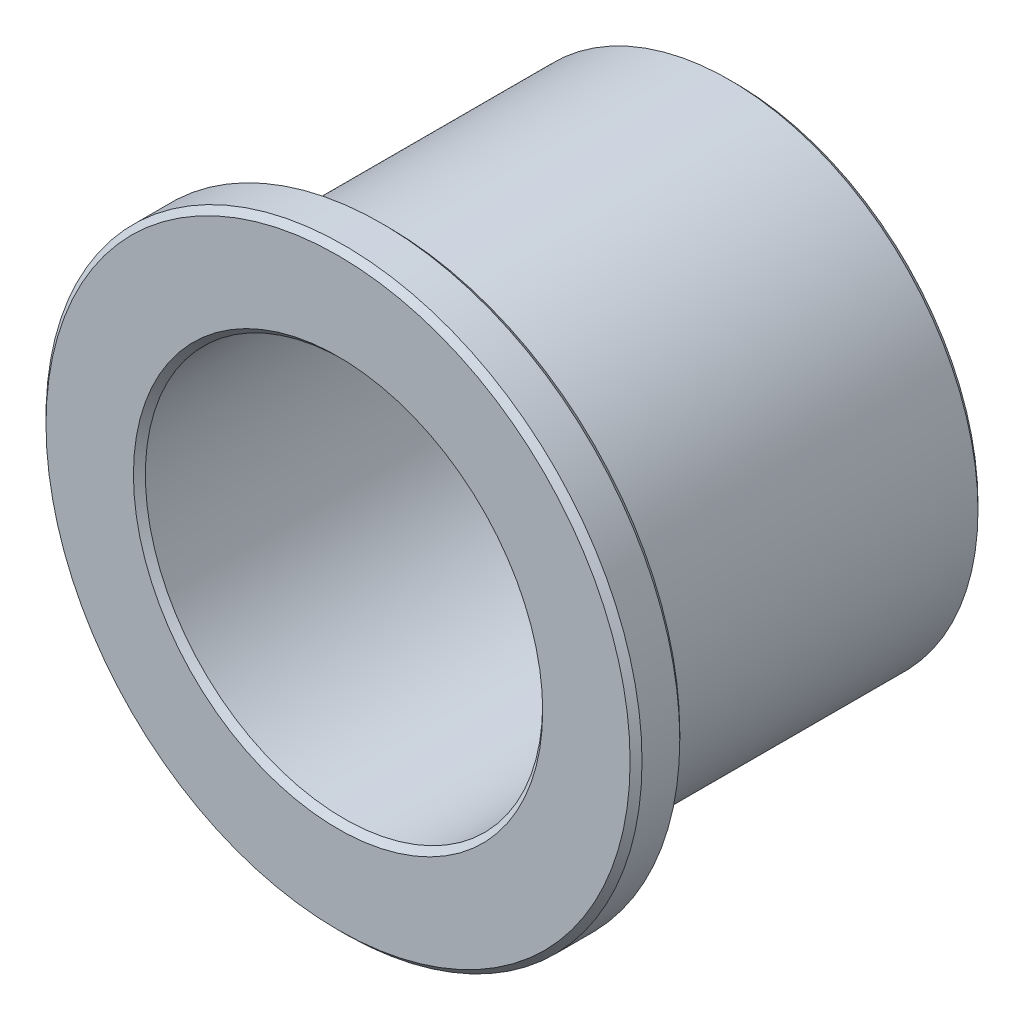
SolidWorks part; units mm, degrees
ref_plane "Front" through (0, 0, 0) normal (0, 0, 1) x (1, 0, 0)
ref_plane "Top" through (0, 0, 0) normal (0, 1, 0) x (1, 0, 0)
ref_plane "Right" through (0, 0, 0) normal (1, 0, 0) x (0, 0, -1)
sketch "Sketch1" plane through (0, 0, 0) normal (0, 0, 1) x (1, 0, 0)
  circle A0 centre (0, 0) radius 12.7
  circle A1 centre (0, 0) radius 15.8877
  circle A2 centre (0, 0) radius 19.05
  dimension "ID" = 25.4
  dimension "OD" = 31.7754
  dimension "Flange OD" = 38.1
sketch "Sketch2" plane through (0, 0, 0) normal (1, 0, 0) x (0, 0, -1)
  line L0 (-12.7, -19.05) -> (12.7, -19.05) construction
  line L1 (0, 19.05) -> (0, -19.05) construction
  line L3 (-9.525, 15.8877) -> (12.7, 15.8877) construction
  point P3 (0, -19.05)
  point P7 (0, 15.8877)
  point P9 (-9.525, -19.05)
  point P10 (-12.7, 19.05)
  point P23 (0, 19.05)
  dimension "Flange Thickness" = 3.175
  dimension "Length" = 25.4
sketch "Sketch3" plane through (0, 0, 0) normal (0, 0, 1) x (1, 0, 0)
  circle A0 centre (0, 0) radius 19.05 construction
  circle A1 centre (0, 0) radius 19.05
  circle A2 centre (0, 0) radius 12.7 construction
  circle A3 centre (0, 0) radius 12.7
extrude "Boss-Extrude1" add sketch "Sketch3" against normal up to vertex (-9.525 mm away) from vertex at 12.7 starting at point (0, -19.05, 12.7)
sketch "Sketch4" plane through (0, 0, 0) normal (0, 0, 1) x (1, 0, 0)
  circle A0 centre (0, 0) radius 12.7 construction
  circle A1 centre (0, 0) radius 15.8877 construction
  circle A2 centre (0, 0) radius 12.7
  circle A3 centre (0, 0) radius 15.8877
extrude "Boss-Extrude2" add sketch "Sketch4" against normal up to vertex (12.7 mm away) from vertex at 9.525 starting at point (0, -19.05, 9.525)
chamfer "Chamfer1" distance 0.381 angle 45 6 edges at (12.7, 0, 12.7) (19.05, 0, 12.7) (19.05, 0, 9.525) (15.8877, 0, 9.525) (12.7, 0, -12.7) (15.8877, 0, -12.7)
equation "\"D1@Chamfer1\"=\"ID@Sketch1\"*0.015"
